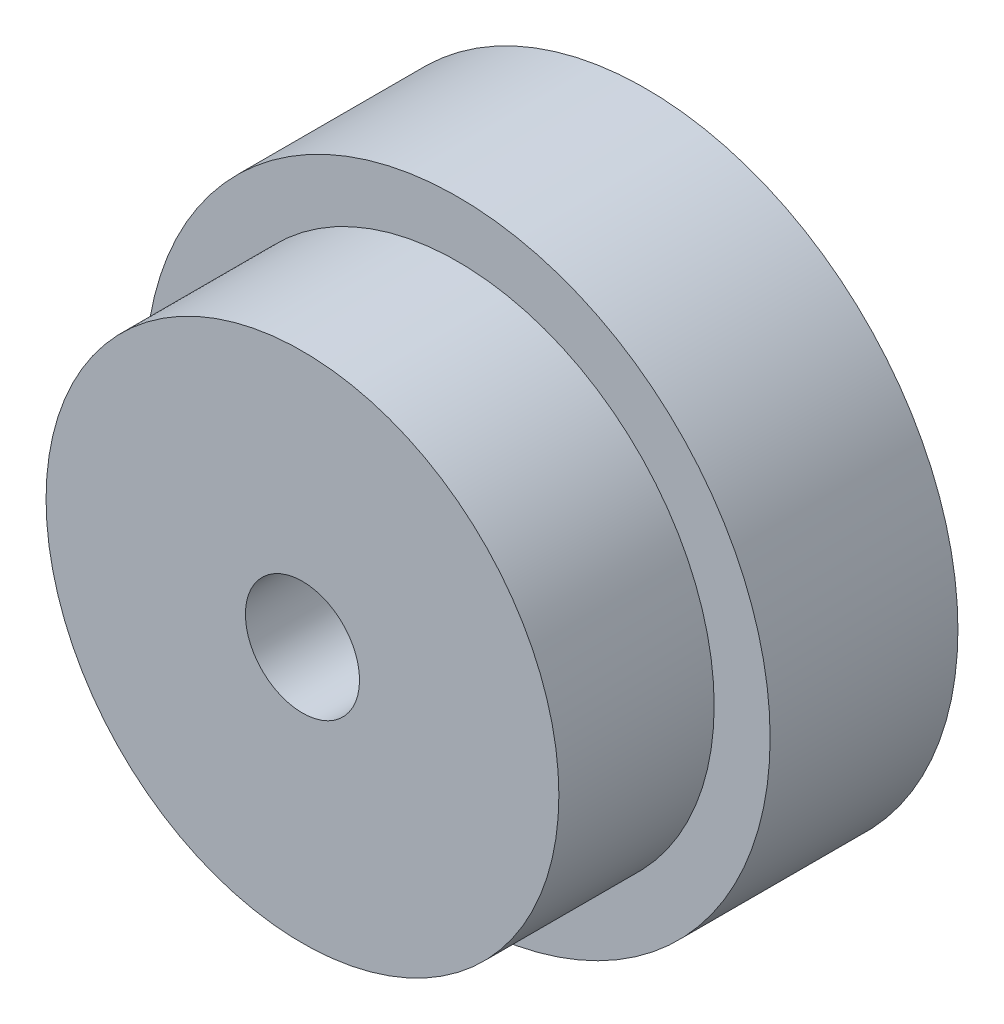
SolidWorks part; units mm, degrees
ref_plane "Front Plane" through (0, 0, 0) normal (0, 0, 1) x (1, 0, 0)
ref_plane "Top Plane" through (0, 0, 0) normal (0, 1, 0) x (1, 0, 0)
ref_plane "Right Plane" through (0, 0, 0) normal (1, 0, 0) x (0, 0, -1)
sketch "Sketch1" plane through (0, 0, 0) normal (0, 0, 1) x (1, 0, 0)
  circle A0 centre (0, 0) radius 10.9855
  dimension "D1" = 21.971
extrude "Boss-Extrude1" add sketch "Sketch1" along normal blind 6.604 contours A0
sketch "Sketch2" plane through (0, 0, 6.604) normal (0, 0, 1) x (1, 0, 0)
  circle A0 centre (0, 0) radius 9.017
  dimension "D1" = 18.034
extrude "Boss-Extrude2" add sketch "Sketch2" along normal blind 5.461 contours A0
sketch "Sketch3" plane through (0, 0, 12.065) normal (0, 0, 1) x (1, 0, 0)
  circle A0 centre (0, 0) radius 2.0066
  dimension "D1" = 4.0132
extrude "Cut-Extrude1" cut sketch "Sketch3" against normal through all contours A0
